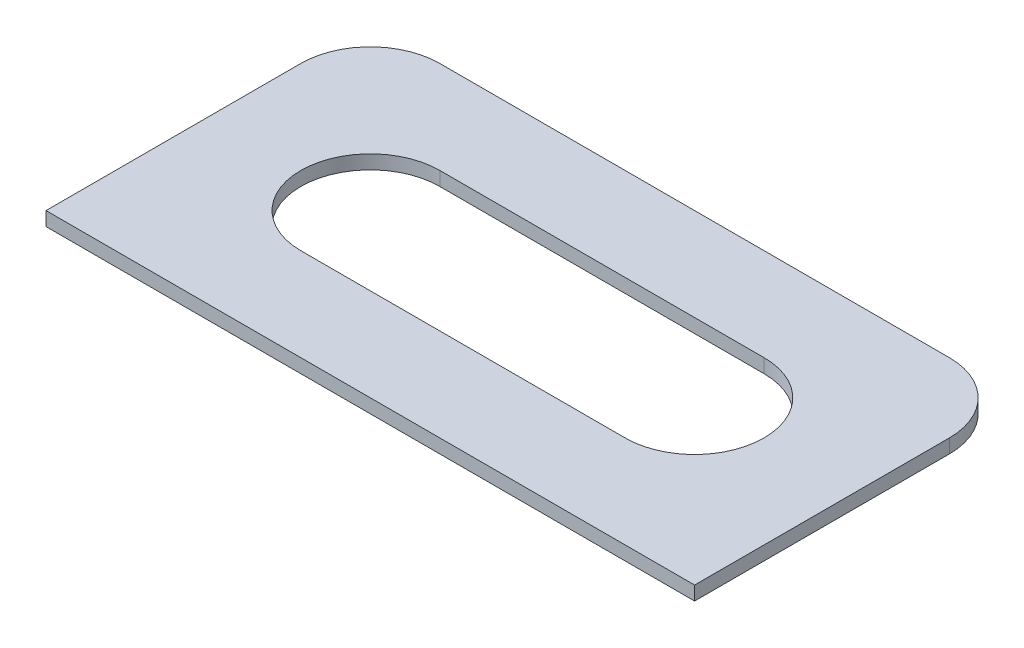
SolidWorks part; units mm, degrees
ref_plane "Plan de face" through (0, 0, 0) normal (0, 0, 1) x (1, 0, 0)
ref_plane "Plan de dessus" through (0, 0, 0) normal (0, 1, 0) x (1, 0, 0)
ref_plane "Plan de droite" through (0, 0, 0) normal (1, 0, 0) x (0, 0, -1)
sketch "Esquisse3" plane through (0, 0, 0) normal (0, 1, 0) x (1, 0, 0)
  line L0 (-45, 77.5166) -> (-45, -49.6358) construction
  line L1 (-65, 21.652) -> (45, 21.652)
  line L2 (-80, 6.652) -> (-80, -48.348)
  line L3 (-80, -48.348) -> (60, -48.348)
  line L4 (60, 6.652) -> (60, -48.348)
  line L5 (-80, 21.652) -> (60, -48.348) construction
  line L6 (-80, -48.348) -> (60, 21.652) construction
  line L7 (25, 38.4365) -> (25, -65.1325) construction
  line L8 (-45, -13.348) -> (25, -13.348) construction
  line L9 (-45, 1.652) -> (25, 1.652)
  line L10 (-45, -28.348) -> (25, -28.348)
  arc A0 (-45, 1.652) -> (-45, -28.348) centre (-45, -13.348) ccw
  arc A1 (25, -28.348) -> (25, 1.652) centre (25, -13.348) ccw
  arc A2 (45, 21.652) -> (60, 6.652) centre (45, 6.652) cw
  arc A3 (-65, 21.652) -> (-80, 6.652) centre (-65, 6.652) ccw
  point P0 (-10, -13.348)
  point P12 (-10, -13.348)
  point P17 (0, 0)
  point P25 (0, 0)
  dimension "D5" = 15
  dimension "D6" = 15
  dimension "D1" = 70
  dimension "D2" = 140
  dimension "D3" = 35
  dimension "D4" = 35
extrude "Boss.-Extru.1" add sketch "Esquisse3" along normal blind 3
